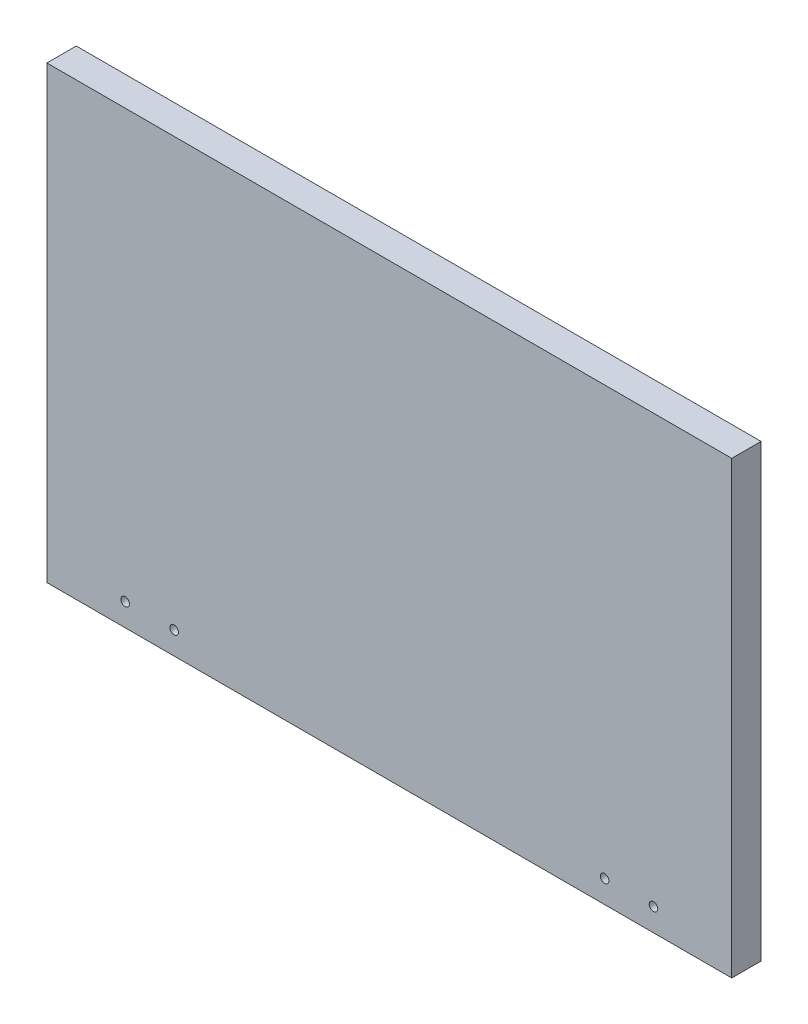
SolidWorks part; units mm, degrees
ref_plane "Front Plane" through (0, 0, 0) normal (0, 0, 1) x (1, 0, 0)
ref_plane "Top Plane" through (0, 0, 0) normal (0, 1, 0) x (1, 0, 0)
ref_plane "Right Plane" through (0, 0, 0) normal (1, 0, 0) x (0, 0, -1)
sketch "Sketch1" plane through (0, 0, 0) normal (0, 0, 1) x (1, 0, 0)
  line L1 (-175, 115) -> (175, 115)
  line L2 (-175, 115) -> (-175, -115)
  line L3 (-175, -115) -> (175, -115)
  line L4 (175, 115) -> (175, -115)
  line L5 (-175, 115) -> (175, -115) construction
  line L6 (-175, -115) -> (175, 115) construction
  point P0 (0, 0)
  dimension "D1" = 350
  dimension "D2" = 230
extrude "Boss-Extrude1" add sketch "Sketch1" along normal blind 15
sketch "Sketch2" plane through (0, 0, 0) normal (0, 0, -1) x (-1, 0, 0)
  line L0 (175, 115) -> (175, -115) construction
  line L1 (175, -115) -> (-175, -115) construction
  line L2 (-175, -115) -> (-175, 115) construction
  circle A0 centre (135, -103.4) radius 2.2
  circle A1 centre (110, -103.4) radius 2.2
  circle A2 centre (-135, -103.4) radius 2.2
  circle A3 centre (-110, -103.4) radius 2.2
  dimension "D1" = 4.4
  dimension "D5" = 4.4
  dimension "D2" = 40
  dimension "D3" = 11.6
  dimension "D6" = 11.6
  dimension "D7" = 40
  dimension "D4" = 2
  dimension "D8" = 2
extrude "Cut-Extrude1" cut sketch "Sketch2" against normal through all
